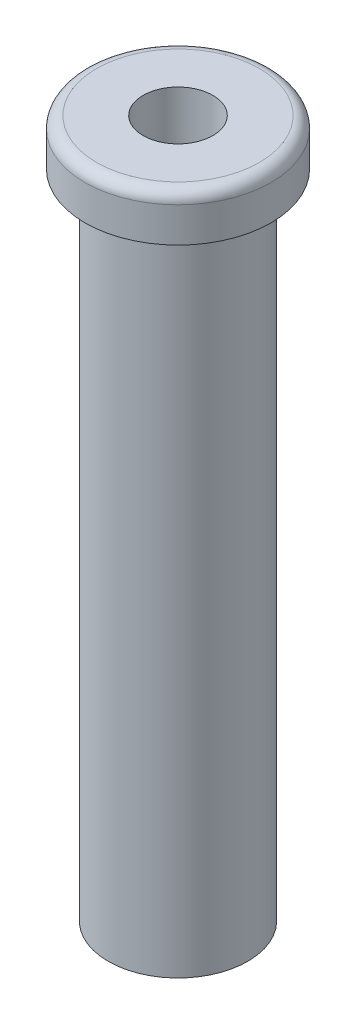
SolidWorks part; units mm, degrees
ref_plane "Piano frontale" through (0, 0, 0) normal (0, 0, 1) x (1, 0, 0)
ref_plane "Piano superiore" through (0, 0, 0) normal (0, 1, 0) x (1, 0, 0)
ref_plane "Piano destro" through (0, 0, 0) normal (1, 0, 0) x (0, 0, -1)
sketch "Schizzo1" plane through (0, 0, 0) normal (0, 1, 0) x (1, 0, 0)
  circle A0 centre (0, 0) radius 6
  circle A1 centre (0, 0) radius 3
  dimension "D1" = 12
  dimension "D2" = 6
extrude "Estrusione-Estrusione1" add sketch "Schizzo1" along normal blind 56
sketch "Schizzo2" plane through (0, 56, 0) normal (0, 1, 0) x (1, 0, 0)
  circle A0 centre (0, 0) radius 3
  circle A1 centre (0, 0) radius 8
  circle A2 centre (0, 0) radius 3 construction
  dimension "D1" = 16
extrude "Estrusione-Estrusione2" add sketch "Schizzo2" along normal blind 4
fillet "Raccordo1" radius 1 1 edges at (0, 60, 8)
